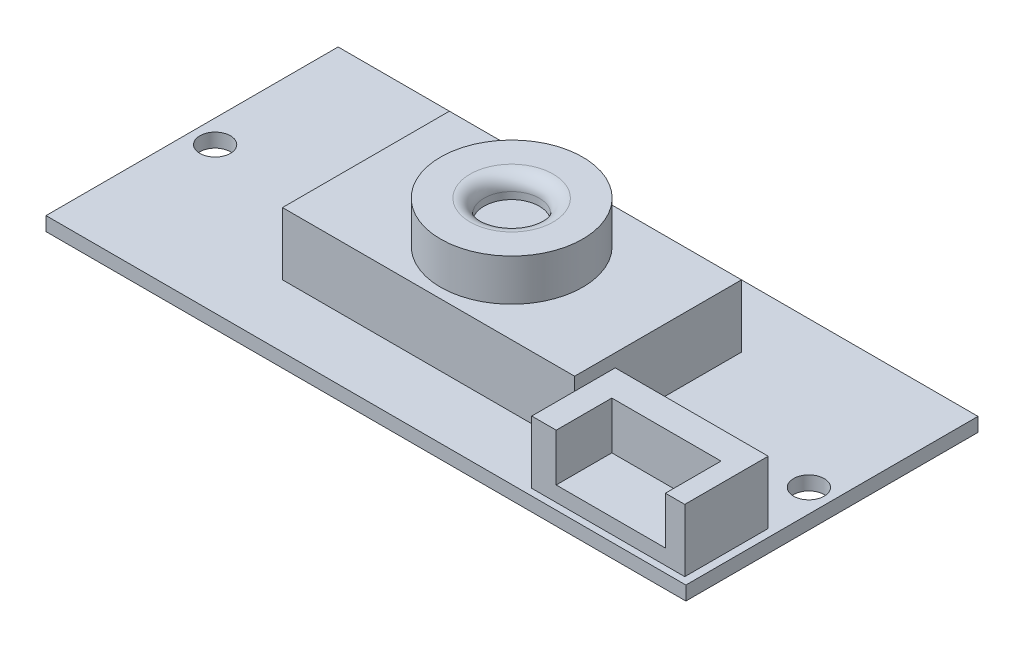
SolidWorks part; units mm, degrees
ref_plane "Front Plane" through (0, 0, 0) normal (0, 0, 1) x (1, 0, 0)
ref_plane "Top Plane" through (0, 0, 0) normal (0, 1, 0) x (1, 0, 0)
ref_plane "Right Plane" through (0, 0, 0) normal (1, 0, 0) x (0, 0, -1)
sketch "Sketch1" plane through (0, 0, 0) normal (0, 1, 0) x (1, 0, 0)
  line L1 (0, 0) -> (46, 0)
  line L2 (0, 0) -> (0, -21)
  line L3 (0, -21) -> (46, -21)
  line L4 (46, 0) -> (46, -21)
  dimension "D1" = 46
  dimension "D2" = 21
extrude "Boss-Extrude1" add sketch "Sketch1" along normal blind 1
sketch "Sketch2" plane through (0, 1, 0) normal (0, 1, 0) x (1, 0, 0)
  line L0 (23, -4.5) -> (23, 0) construction
  line L1 (12.5, -4.5) -> (33.5, -4.5)
  line L2 (12.5, -4.5) -> (12.5, -16.5)
  line L3 (12.5, -16.5) -> (33.5, -16.5)
  line L4 (33.5, -4.5) -> (33.5, -16.5)
  line L5 (46, 0) -> (0, 0) construction
  line L6 (33.5, -10.5) -> (46, -10.5) construction
  line L7 (46, -21) -> (46, 0) construction
  line L8 (23, -16.5) -> (23, -21) construction
  line L9 (0, -21) -> (46, -21) construction
  line L10 (12.5, -10.5) -> (0, -10.5) construction
  line L11 (0, 0) -> (0, -21) construction
  line L13 (34.4396, -14.5205) -> (45.4396, -14.5205)
  line L14 (34.4396, -14.5205) -> (34.4396, -20.5205)
  line L15 (34.4396, -20.5205) -> (45.4396, -20.5205)
  line L16 (45.4396, -14.5205) -> (45.4396, -20.5205)
  dimension "D1" = 21
  dimension "D2" = 12
  dimension "D3" = 11
  dimension "D4" = 6
extrude "Boss-Extrude2" add sketch "Sketch2" along normal blind 4.5
sketch "Sketch3" plane through (0, 0, 20.5205) normal (0, 0, 1) x (1, 0, 0)
  line L0 (34.4396, 5.5) -> (45.4396, 5.5) construction
  line L1 (36.1976, 5.5) -> (44.0475, 5.5)
  line L2 (36.1976, 5.5) -> (36.1976, 2.0877)
  line L3 (36.1976, 2.0877) -> (44.0475, 2.0877)
  line L4 (44.0475, 5.5) -> (44.0475, 2.0877)
extrude "Cut-Extrude1" cut sketch "Sketch3" against normal blind 4
sketch "Sketch4" plane through (0, 5.5, 0) normal (0, 1, 0) x (1, 0, 0)
  circle A0 centre (23.1472, -10.6717) radius 5.1093
extrude "Boss-Extrude3" add sketch "Sketch4" along normal blind 3
sketch "Sketch5" plane through (0, 8.5, 0) normal (0, 1, 0) x (1, 0, 0)
  circle A0 centre (23.1472, -10.6717) radius 1.9868
extrude "Cut-Extrude2" cut sketch "Sketch5" against normal blind 1.5
fillet "Fillet1" radius 1 1 edges at (23.1472, 8.5, 12.6586)
sketch "Sketch6" plane through (0, 1, 0) normal (0, 1, 0) x (1, 0, 0)
  line L0 (1.6582, -21) -> (1.6582, 0) construction
  line L1 (0, -21) -> (46, -21) construction
  line L2 (46, 0) -> (0, 0) construction
  line L3 (44.3418, 0) -> (44.3418, -21) construction
  circle A1 centre (1.6582, -10.5) radius 1.1
  circle A2 centre (44.3418, -10.5) radius 1.1
  dimension "D1" = 2.2
  dimension "D2" = 2.2
extrude "Cut-Extrude3" cut sketch "Sketch6" against normal blind 1.5
